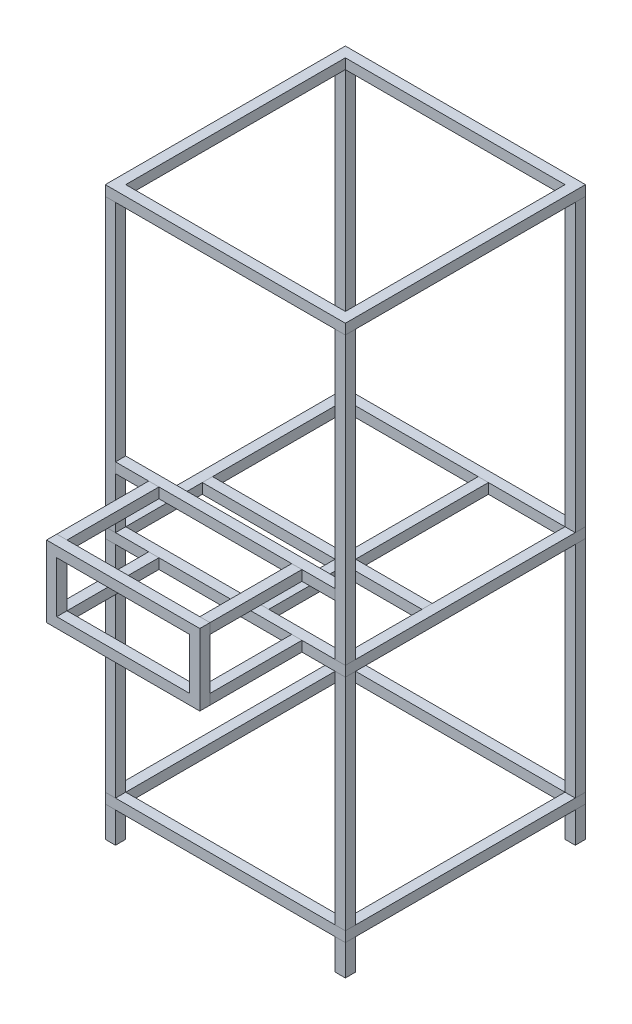
SolidWorks part; units mm, degrees
ref_plane "정면" through (0, 0, 0) normal (0, 0, 1) x (1, 0, 0)
ref_plane "윗면" through (0, 0, 0) normal (0, 1, 0) x (1, 0, 0)
ref_plane "우측면" through (0, 0, 0) normal (1, 0, 0) x (0, 0, -1)
sketch "스케치1" plane through (0, 0, 0) normal (0, 1, 0) x (1, 0, 0)
  line L1 (0, 0) -> (470, 0)
  line L2 (0, 0) -> (0, 470)
  line L3 (0, 470) -> (470, 470)
  line L4 (470, 0) -> (470, 470)
  line L5 (450, 450) -> (20, 450)
  line L6 (450, 450) -> (450, 20)
  line L7 (450, 20) -> (20, 20)
  line L8 (20, 450) -> (20, 20)
  dimension "D1" = 470
  dimension "D2" = 470
  dimension "D3" = 430
  dimension "D4" = 430
  dimension "D5" = 20
  dimension "D6" = 20
extrude "보스-돌출1" add sketch "스케치1" against normal blind 20
sketch "스케치2" plane through (0, -20, 0) normal (0, -1, 0) x (1, 0, 0)
  line L1 (0, 0) -> (20, 0)
  line L2 (0, 0) -> (0, -20)
  line L3 (0, -20) -> (20, -20)
  line L4 (20, 0) -> (20, -20)
  line L5 (470, 0) -> (450, 0)
  line L6 (470, 0) -> (470, -20)
  line L7 (470, -20) -> (450, -20)
  line L8 (450, 0) -> (450, -20)
  line L9 (450, -450) -> (470, -450)
  line L10 (450, -450) -> (450, -470)
  line L11 (450, -470) -> (470, -470)
  line L12 (470, -450) -> (470, -470)
  line L13 (20, -450) -> (0, -450)
  line L14 (20, -450) -> (20, -470)
  line L15 (20, -470) -> (0, -470)
  line L16 (0, -450) -> (0, -470)
extrude "보스-돌출2" add sketch "스케치2" along normal blind 560 separate body
ref_plane "평면1" through (0, -600, 0) normal (0, 1, 0) x (1, 0, 0)
ref_plane "평면2" through (0, -1030, 0) normal (0, 1, 0) x (1, 0, 0)
sketch "스케치3" plane through (0, -1030, 0) normal (0, 1, 0) x (1, 0, 0)
  line L1 (0, 0) -> (470, 0)
  line L2 (0, 0) -> (0, 470)
  line L3 (0, 470) -> (470, 470)
  line L4 (470, 0) -> (470, 470)
  line L5 (20, 20) -> (450, 20)
  line L6 (20, 20) -> (20, 450)
  line L7 (20, 450) -> (450, 450)
  line L8 (450, 20) -> (450, 450)
extrude "보스-돌출3" add sketch "스케치3" against normal blind 20 separate body
sketch "스케치4" plane through (0, -600, 0) normal (0, 1, 0) x (1, 0, 0)
  line L1 (0, 0) -> (470, 0)
  line L2 (0, 0) -> (0, 470)
  line L3 (0, 470) -> (470, 470)
  line L4 (470, 0) -> (470, 470)
  line L5 (450, 450) -> (20, 450)
  line L6 (450, 450) -> (450, 20)
  line L7 (450, 20) -> (20, 20)
  line L8 (20, 450) -> (20, 20)
extrude "보스-돌출4" add sketch "스케치4" along normal blind 20 separate body
sketch "스케치5" plane through (0, -600, 0) normal (0, -1, 0) x (1, 0, 0)
  line L1 (0, 0) -> (20, 0)
  line L2 (0, 0) -> (0, -20)
  line L3 (0, -20) -> (20, -20)
  line L4 (20, 0) -> (20, -20)
  line L5 (450, -20) -> (470, -20)
  line L6 (450, -20) -> (450, 0)
  line L7 (450, 0) -> (470, 0)
  line L8 (470, -20) -> (470, 0)
  line L9 (450, -450) -> (470, -450)
  line L10 (450, -450) -> (450, -470)
  line L11 (450, -470) -> (470, -470)
  line L12 (470, -450) -> (470, -470)
  line L13 (20, -450) -> (0, -450)
  line L14 (20, -450) -> (20, -470)
  line L15 (20, -470) -> (0, -470)
  line L16 (0, -450) -> (0, -470)
extrude "보스-돌출5" add sketch "스케치5" along normal up to next (430 mm away) separate body
sketch "스케치6" plane through (0, -1050, 0) normal (0, -1, 0) x (1, 0, 0)
  line L0 (20, -450) -> (20, -20) construction
  line L1 (0, 0) -> (20, 0)
  line L2 (0, 0) -> (0, -20)
  line L3 (0, -20) -> (20, -20)
  line L4 (20, 0) -> (20, -20)
  line L5 (20, -20) -> (450, -20) construction
  line L7 (450, -20) -> (470, -20)
  line L8 (450, -20) -> (450, 0)
  line L9 (450, 0) -> (470, 0)
  line L10 (470, -20) -> (470, 0)
  line L11 (450, -450) -> (470, -450)
  line L12 (450, -450) -> (450, -470)
  line L13 (450, -470) -> (470, -470)
  line L14 (470, -450) -> (470, -470)
  line L15 (20, -450) -> (0, -450)
  line L16 (20, -450) -> (20, -470)
  line L17 (20, -470) -> (0, -470)
  line L18 (0, -450) -> (0, -470)
extrude "보스-돌출6" add sketch "스케치6" along normal blind 60 separate body
ref_plane "평면3" through (0, -460, 0) normal (0, 1, 0) x (1, 0, 0)
sketch "스케치8" plane through (0, -460, 0) normal (0, 1, 0) x (1, 0, 0)
  line L1 (20, 20) -> (450, 20)
  line L2 (20, 20) -> (20, 0)
  line L3 (20, 0) -> (450, 0)
  line L4 (450, 20) -> (450, 0)
extrude "보스-돌출7" add sketch "스케치8" against normal blind 20 separate body
sketch "스케치9" plane through (0, 0, 0) normal (0, 0, 1) x (1, 0, 0)
  line L0 (20, -460) -> (450, -460) construction
  line L1 (85, -460) -> (385, -460)
  line L2 (85, -460) -> (85, -600)
  line L3 (85, -600) -> (385, -600)
  line L4 (385, -460) -> (385, -600)
  line L5 (0, -600) -> (470, -600) construction
  line L8 (0, -460) -> (470, -460) construction
  line L9 (0, -580) -> (0, -20) construction
  line L10 (470, -580) -> (470, -20) construction
  line L11 (20, -480) -> (450, -480) construction
  line L12 (105, -480) -> (365, -480)
  line L13 (105, -480) -> (105, -580)
  line L14 (105, -580) -> (365, -580)
  line L15 (365, -480) -> (365, -580)
  line L16 (0, -580) -> (470, -580) construction
  point P8 (235, -460)
  dimension "D1" = 300
  dimension "D2" = 20
  dimension "D3" = 20
extrude "보스-돌출8" add sketch "스케치9" along normal blind 20 from offset 180 separate body
sketch "스케치10" plane through (0, 0, 0) normal (0, 0, 1) x (1, 0, 0)
  line L0 (258.5, -460) -> (-258.5, -460) construction
  line L1 (85, -460) -> (105, -460)
  line L2 (85, -460) -> (85, -480)
  line L3 (85, -480) -> (105, -480)
  line L4 (105, -460) -> (105, -480)
  line L5 (365, -480) -> (385, -480)
  line L6 (365, -480) -> (365, -460)
  line L7 (365, -460) -> (385, -460)
  line L8 (385, -480) -> (385, -460)
  line L9 (385, -600) -> (385, -460) construction
  line L11 (365, -580) -> (385, -580)
  line L12 (365, -580) -> (365, -600)
  line L13 (365, -600) -> (385, -600)
  line L14 (385, -580) -> (385, -600)
  line L15 (105, -580) -> (85, -580)
  line L16 (105, -580) -> (105, -600)
  line L17 (105, -600) -> (85, -600)
  line L18 (85, -580) -> (85, -600)
extrude "보스-돌출9" add sketch "스케치10" along normal up to next (180 mm away) separate body
sketch "스케치11" plane through (0, -600, 0) normal (0, -1, 0) x (1, 0, 0)
  line L0 (20, -20) -> (450, -20) construction
  line L1 (280, -20) -> (300, -20)
  line L2 (280, -20) -> (280, -450)
  line L3 (280, -450) -> (300, -450)
  line L4 (300, -20) -> (300, -450)
  line L5 (280, -20) -> (300, -450) construction
  line L6 (280, -450) -> (300, -20) construction
  line L7 (450, -450) -> (20, -450) construction
  line L8 (450, -20) -> (450, -450) construction
  line L9 (450, -190) -> (20, -190)
  line L10 (450, -190) -> (450, -170)
  line L11 (450, -170) -> (20, -170)
  line L12 (20, -190) -> (20, -170)
  line L13 (450, -190) -> (20, -170) construction
  line L14 (450, -170) -> (20, -190) construction
  line L15 (20, -450) -> (20, -20) construction
  point P4 (290, -235)
  point P13 (235, -180)
  dimension "D1" = 20
  dimension "D2" = 20
  dimension "D3" = 150
  dimension "D4" = 150
extrude "보스-돌출10" add sketch "스케치11" against normal blind 20 separate body contours L9 L12 L11 L10 | L2 L3 L4 L1
equation "\"D1@보스-돌출2\"=560"
